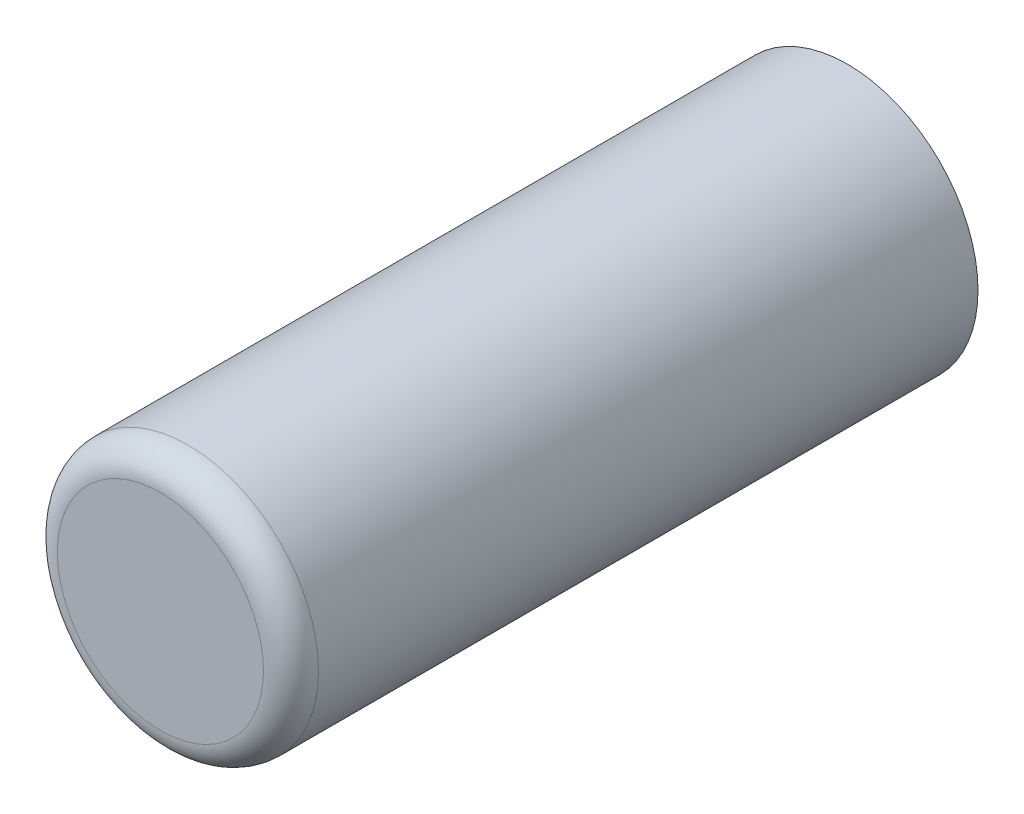
SolidWorks part; units mm, degrees
ref_plane "Front Plane" through (0, 0, 0) normal (0, 0, 1) x (1, 0, 0)
ref_plane "Top Plane" through (0, 0, 0) normal (0, 1, 0) x (1, 0, 0)
ref_plane "Right Plane" through (0, 0, 0) normal (1, 0, 0) x (0, 0, -1)
sketch "Sketch1" plane through (0, 0, 0) normal (0, 0, 1) x (1, 0, 0)
  circle A0 centre (0, 0) radius 3.8
  dimension "D1" = 7.6
extrude "Boss-Extrude1" add sketch "Sketch1" along normal mid plane 20
fillet "Fillet1" radius 0.8 1 edges at (3.8, 0, 10)
